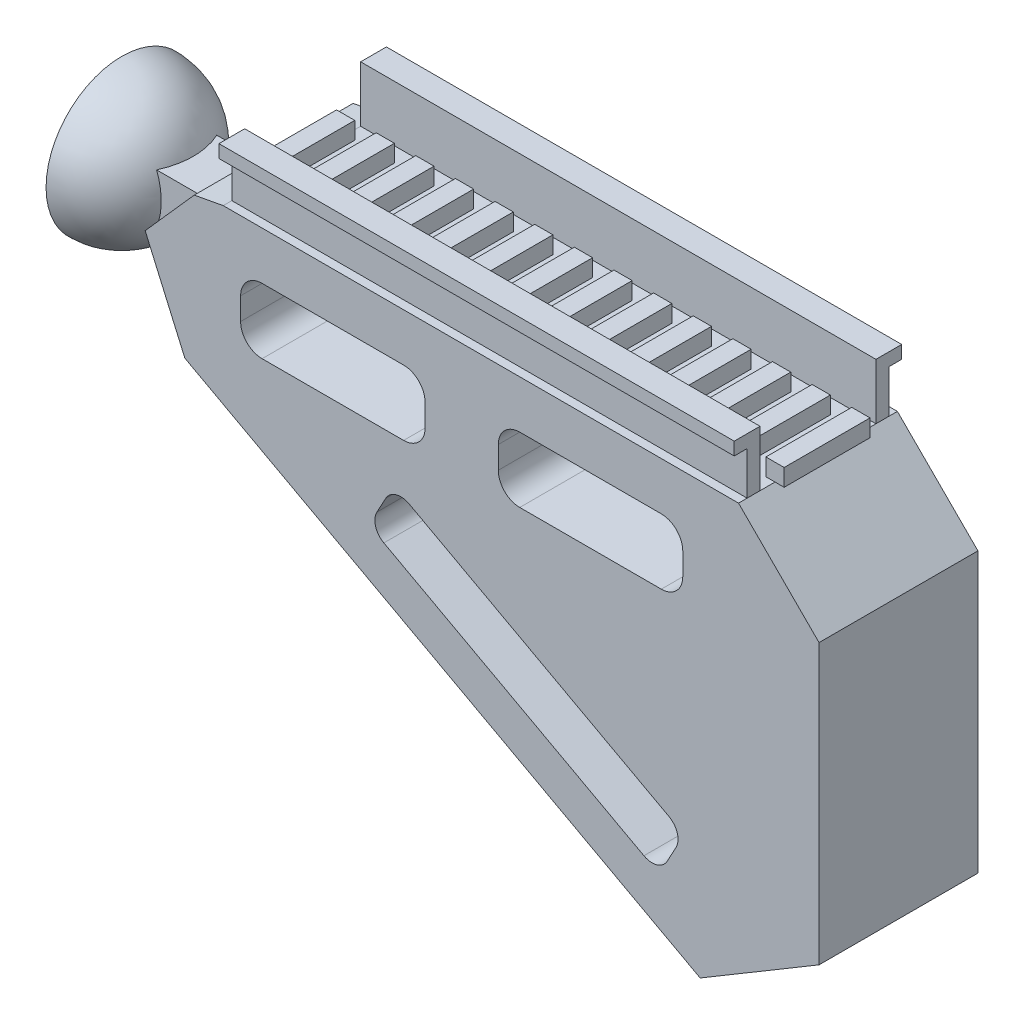
SolidWorks part; units mm, degrees
ref_plane "Front Plane" through (0, 0, 0) normal (0, 0, 1) x (1, 0, 0)
ref_plane "Top Plane" through (0, 0, 0) normal (0, 1, 0) x (1, 0, 0)
ref_plane "Right Plane" through (0, 0, 0) normal (1, 0, 0) x (0, 0, -1)
sketch "Sketch2" plane through (0, 0, 0) normal (1, 0, 0) x (0, 0, -1)
  line L1 (0, 599.7384) -> (0, 1107.4807) construction
sketch "Sketch3" plane through (0, 0, 0) normal (0, 0, 1) x (1, 0, 0)
  line L0 (-305, 571.402) -> (305, 571.402) construction
  point P3 (0, 571.402)
sketch "Sketch8" plane through (0, 0, 0) normal (0, 0, 1) x (1, 0, 0)
  line L0 (0, 18.7499) -> (-119.9998, 18.7499)
  line L5 (-119.9998, 18.7499) -> (-126.7514, 17.4921)
  line L8 (-128.9301, -16.4869) -> (-8.9302, -81.4866)
  line L11 (18.7499, 0) -> (18.7499, -65)
  line L12 (-138.1752, 4.6062) -> (-128.9301, -16.4869)
  line L14 (-8.9302, -81.4866) -> (18.7499, -65)
  line L17 (0, 18.7499) -> (18.7499, 0)
  line L18 (-126.7514, 17.4921) -> (-138.1752, 4.6062)
  dimension "D1" = 119.9998
  dimension "D4" = 18.7499
  dimension "D6" = 16.4866
  dimension "D7" = 27.6801
  dimension "D9" = 65
  dimension "D12" = 9.2451
  dimension "D13" = 12.8859
  dimension "D5" = 18.7499
  dimension "D2" = 65
  dimension "D3" = 119.9998
  dimension "D8" = 18.7499
  dimension "D10" = 64.9998
  dimension "D11" = 21.093
  dimension "D14" = 11.4238
  dimension "D15" = 6.7516
extrude "Boss-Extrude1" add sketch "Sketch8" along normal blind 37
sketch "Sketch10" plane through (0, 0, 0) normal (0, 0, 1) x (1, 0, 0)
  line L0 (-50.9451, -7.596) -> (-17.9852, -7.596)
  line L3 (-110.9451, 7.596) -> (-77.9852, 7.596)
  line L6 (-12.9852, 2.596) -> (-12.9852, -2.596)
  line L11 (-115.9451, 2.596) -> (-115.9451, -2.596)
  line L12 (-110.9451, -7.596) -> (-77.9852, -7.596)
  line L13 (-72.9852, 2.596) -> (-72.9852, -2.596)
  line L14 (-50.9451, 7.596) -> (-17.9852, 7.596)
  line L15 (-55.9451, 2.596) -> (-55.9451, -2.596)
  arc A8 (-110.9451, 7.596) -> (-115.9451, 2.596) centre (-110.9451, 2.596) ccw
  arc A9 (-77.9852, 7.596) -> (-72.9852, 2.596) centre (-77.9852, 2.596) cw
  arc A10 (-77.9852, -7.596) -> (-72.9852, -2.596) centre (-77.9852, -2.596) ccw
  arc A11 (-115.9451, -2.596) -> (-110.9451, -7.596) centre (-110.9451, -2.596) ccw
  arc A12 (-17.9852, -7.596) -> (-12.9852, -2.596) centre (-17.9852, -2.596) ccw
  arc A13 (-17.9852, 7.596) -> (-12.9852, 2.596) centre (-17.9852, 2.596) cw
  arc A14 (-50.9451, 7.596) -> (-55.9451, 2.596) centre (-50.9451, 2.596) ccw
  arc A15 (-55.9451, -2.596) -> (-50.9451, -7.596) centre (-50.9451, -2.596) ccw
  dimension "D3" = 5
  dimension "D4" = 5
  dimension "D5" = 5.1921
  dimension "D6" = 32.9598
  dimension "D2" = 7.596
  dimension "D8" = 27.0402
  dimension "D1" = 77.9852
  dimension "D7" = 2
extrude "Cut-Extrude1" cut sketch "Sketch10" against normal blind 1 and the other way up to surface (37 mm away) other way up to face at (-60.6609, -12.9219, 37)
ref_plane "Plane1" through (0, 18.7499, 0) normal (0, 1, 0) x (1, 0, 0)
sketch "Sketch13" plane through (0, 18.7499, 0) normal (0, 1, 0) x (1, 0, 0)
  line L1 (-2.125, -8.5) -> (2.125, -8.5)
  line L2 (-2.125, -8.5) -> (-2.125, -28.5)
  line L3 (-2.125, -28.5) -> (2.125, -28.5)
  line L4 (2.125, -8.5) -> (2.125, -28.5)
  line L5 (-2.125, -8.5) -> (2.125, -28.5) construction
  line L6 (-2.125, -28.5) -> (2.125, -8.5) construction
  line L7 (-11.355, -8.5) -> (-7.105, -8.5)
  line L8 (-11.355, -8.5) -> (-11.355, -28.5)
  line L9 (-11.355, -28.5) -> (-7.105, -28.5)
  line L10 (-7.105, -8.5) -> (-7.105, -28.5)
  line L11 (-11.355, -8.5) -> (-7.105, -28.5) construction
  line L12 (-11.355, -28.5) -> (-7.105, -8.5) construction
  line L13 (-20.585, -8.5) -> (-16.335, -8.5)
  line L14 (-20.585, -8.5) -> (-20.585, -28.5)
  line L15 (-20.585, -28.5) -> (-16.335, -28.5)
  line L16 (-16.335, -8.5) -> (-16.335, -28.5)
  line L17 (-20.585, -8.5) -> (-16.335, -28.5) construction
  line L18 (-20.585, -28.5) -> (-16.335, -8.5) construction
  line L19 (-29.815, -8.5) -> (-25.565, -8.5)
  line L20 (-29.815, -8.5) -> (-29.815, -28.5)
  line L21 (-29.815, -28.5) -> (-25.565, -28.5)
  line L22 (-25.565, -8.5) -> (-25.565, -28.5)
  line L23 (-29.815, -8.5) -> (-25.565, -28.5) construction
  line L24 (-29.815, -28.5) -> (-25.565, -8.5) construction
  line L25 (-39.045, -8.5) -> (-34.795, -8.5)
  line L26 (-39.045, -8.5) -> (-39.045, -28.5)
  line L27 (-39.045, -28.5) -> (-34.795, -28.5)
  line L28 (-34.795, -8.5) -> (-34.795, -28.5)
  line L29 (-39.045, -8.5) -> (-34.795, -28.5) construction
  line L30 (-39.045, -28.5) -> (-34.795, -8.5) construction
  line L31 (-48.275, -8.5) -> (-44.025, -8.5)
  line L32 (-48.275, -8.5) -> (-48.275, -28.5)
  line L33 (-48.275, -28.5) -> (-44.025, -28.5)
  line L34 (-44.025, -8.5) -> (-44.025, -28.5)
  line L35 (-48.275, -8.5) -> (-44.025, -28.5) construction
  line L36 (-48.275, -28.5) -> (-44.025, -8.5) construction
  line L37 (-57.505, -8.5) -> (-53.255, -8.5)
  line L38 (-57.505, -8.5) -> (-57.505, -28.5)
  line L39 (-57.505, -28.5) -> (-53.255, -28.5)
  line L40 (-53.255, -8.5) -> (-53.255, -28.5)
  line L41 (-57.505, -8.5) -> (-53.255, -28.5) construction
  line L42 (-57.505, -28.5) -> (-53.255, -8.5) construction
  line L43 (-66.735, -8.5) -> (-62.485, -8.5)
  line L44 (-66.735, -8.5) -> (-66.735, -28.5)
  line L45 (-66.735, -28.5) -> (-62.485, -28.5)
  line L46 (-62.485, -8.5) -> (-62.485, -28.5)
  line L47 (-66.735, -8.5) -> (-62.485, -28.5) construction
  line L48 (-66.735, -28.5) -> (-62.485, -8.5) construction
  line L49 (-75.965, -8.5) -> (-71.715, -8.5)
  line L50 (-75.965, -8.5) -> (-75.965, -28.5)
  line L51 (-75.965, -28.5) -> (-71.715, -28.5)
  line L52 (-71.715, -8.5) -> (-71.715, -28.5)
  line L53 (-75.965, -8.5) -> (-71.715, -28.5) construction
  line L54 (-75.965, -28.5) -> (-71.715, -8.5) construction
  line L55 (-85.195, -8.5) -> (-80.945, -8.5)
  line L56 (-85.195, -8.5) -> (-85.195, -28.5)
  line L57 (-85.195, -28.5) -> (-80.945, -28.5)
  line L58 (-80.945, -8.5) -> (-80.945, -28.5)
  line L59 (-85.195, -8.5) -> (-80.945, -28.5) construction
  line L60 (-85.195, -28.5) -> (-80.945, -8.5) construction
  line L61 (-94.425, -8.5) -> (-90.175, -8.5)
  line L62 (-94.425, -8.5) -> (-94.425, -28.5)
  line L63 (-94.425, -28.5) -> (-90.175, -28.5)
  line L64 (-90.175, -8.5) -> (-90.175, -28.5)
  line L65 (-94.425, -8.5) -> (-90.175, -28.5) construction
  line L66 (-94.425, -28.5) -> (-90.175, -8.5) construction
  line L67 (-103.655, -8.5) -> (-99.405, -8.5)
  line L68 (-103.655, -8.5) -> (-103.655, -28.5)
  line L69 (-103.655, -28.5) -> (-99.405, -28.5)
  line L70 (-99.405, -8.5) -> (-99.405, -28.5)
  line L71 (-103.655, -8.5) -> (-99.405, -28.5) construction
  line L72 (-103.655, -28.5) -> (-99.405, -8.5) construction
  line L73 (-112.885, -8.5) -> (-108.635, -8.5)
  line L74 (-112.885, -8.5) -> (-112.885, -28.5)
  line L75 (-112.885, -28.5) -> (-108.635, -28.5)
  line L76 (-108.635, -8.5) -> (-108.635, -28.5)
  line L77 (-112.885, -8.5) -> (-108.635, -28.5) construction
  line L78 (-112.885, -28.5) -> (-108.635, -8.5) construction
  line L79 (-122.115, -8.5) -> (-117.865, -8.5)
  line L80 (-122.115, -8.5) -> (-122.115, -28.5)
  line L81 (-122.115, -28.5) -> (-117.865, -28.5)
  line L82 (-117.865, -8.5) -> (-117.865, -28.5)
  line L83 (-122.115, -8.5) -> (-117.865, -28.5) construction
  line L84 (-122.115, -28.5) -> (-117.865, -8.5) construction
  point P0 (0, -18.5)
  point P9 (-9.23, -18.5)
  point P14 (-18.46, -18.5)
  point P19 (-27.69, -18.5)
  point P24 (-36.92, -18.5)
  point P29 (-46.15, -18.5)
  point P34 (-55.38, -18.5)
  point P39 (-64.61, -18.5)
  point P44 (-73.84, -18.5)
  point P49 (-83.07, -18.5)
  point P54 (-92.3, -18.5)
  point P59 (-101.53, -18.5)
  point P64 (-110.76, -18.5)
  point P69 (-119.99, -18.5)
  dimension "D1" = 4.25
  dimension "D2" = 20
  dimension "D4" = 2.125
  dimension "D5" = 8.5
  dimension "D6" = 4.98
  dimension "D3" = 14
extrude "Boss-Extrude3" add sketch "Sketch13" along normal blind 4 from surface at 0 starting at face at (-59.9999, 18.7499, 18.5)
ref_plane "Plane2" through (-132.115, 0, 0) normal (-1, 0, 0) x (0, 0, 1)
ref_plane "Plane3" through (-162.115, 0, 0) normal (-1, 0, 0) x (0, 0, 1)
sketch "Sketch23" plane through (-162.115, 0, 0) normal (-1, 0, 0) x (0, 0, 1)
  line L0 (18.5023, 18.5528) -> (18.5023, 15.1814)
  line L1 (18.5023, -13.3454) -> (18.5023, -16.7168)
  line L2 (18.5023, 19.7198) -> (18.5023, -18.316) construction
  arc A2 (18.5023, 15.1814) -> (18.5023, -13.3454) centre (18.5023, 0.918) ccw
  arc A3 (18.5023, -16.7168) -> (18.5023, 18.5528) centre (18.5023, 0.918) cw
  point P2 (0.8675, 0.918)
  dimension "D1" = 18.5528
  dimension "D2" = 18.5023
  dimension "D4" = 14.2634
  dimension "D5" = 17.6348
  dimension "D3" = 3.3714
  dimension "D6" = 3.3714
  dimension "D7" = 18.5023
  dimension "D8" = 28.5269
  dimension "D9" = 17.6348
revolve "Revolve4" add sketch "Sketch23" angle 180 about L2
sketch "Sketch24" plane through (-132.115, 0, 0) normal (-1, 0, 0) x (0, 0, 1)
  line L0 (18.5023, 200019.7198) -> (18.5023, -200018.316) construction
  line L1 (11.5023, 6.7019) -> (25.5023, 6.7019)
  line L2 (11.5023, 6.7019) -> (11.5023, -5.2981)
  line L3 (11.5023, -5.2981) -> (25.5023, -5.2981)
  line L4 (25.5023, 6.7019) -> (25.5023, -5.2981)
  line L5 (11.5023, 6.7019) -> (25.5023, -5.2981) construction
  line L6 (11.5023, -5.2981) -> (25.5023, 6.7019) construction
  point P0 (18.5023, 0.7019)
  dimension "D1" = 12
  dimension "D2" = 14
extrude "Boss-Extrude5" add sketch "Sketch24" along normal up to surface (14.8827 mm away)
sketch "Sketch25" plane through (0, 0, 0) normal (1, 0, 0) x (0, 0, -1)
  line L0 (-32, 31.7499) -> (-32, 18.7499)
  line L1 (-18.5, 18.6291) -> (-18.5, 40.0374) construction
  line L2 (-35, 18.7499) -> (-35, 28.7499)
  line L4 (-35, 28.7499) -> (-38, 28.7499)
  line L5 (-38, 28.7499) -> (-38, 31.7499)
  line L6 (-38, 31.7499) -> (-32, 31.7499)
  line L8 (1, 31.7499) -> (-5, 31.7499)
  line L9 (1, 28.7499) -> (1, 31.7499)
  line L10 (-2, 28.7499) -> (1, 28.7499)
  line L11 (-2, 18.7499) -> (-2, 28.7499)
  line L12 (-5, 31.7499) -> (-5, 18.7499)
  line L13 (-35, 18.7499) -> (-32, 18.7499)
  line L14 (-5, 18.7499) -> (-2, 18.7499)
  dimension "D1" = 13
  dimension "D2" = 6
  dimension "D3" = 3
  dimension "D4" = 3
  dimension "D5" = 32
  dimension "D6" = 18.7499
  dimension "D7" = 13.5
extrude "Boss-Extrude6" add sketch "Sketch25" against normal blind 120
sketch "Sketch26" plane through (0, 0, 0) normal (0, 0, 1) x (1, 0, 0)
  line L1 (-128.9301, -16.4869) -> (-8.9302, -81.4866) construction
  line L2 (-68.9302, -48.9867) -> (-54.2673, -21.9168) construction
  line L3 (-82.1572, -21.3719) -> (-84.2052, -25.1528)
  line L4 (-82.5931, -30.5751) -> (-22.0305, -63.3798)
  line L5 (-16.6082, -61.7678) -> (-14.5602, -57.9868)
  line L6 (-16.1723, -52.5645) -> (-76.7349, -19.7598)
  arc A0 (-22.0305, -63.3798) -> (-16.6082, -61.7678) centre (-20.1254, -59.8626) ccw
  arc A1 (-14.5602, -57.9868) -> (-16.1723, -52.5645) centre (-18.0774, -56.0817) ccw
  arc A2 (-84.2052, -25.1528) -> (-82.5931, -30.5751) centre (-80.688, -27.058) ccw
  arc A3 (-76.7349, -19.7598) -> (-82.1572, -21.3719) centre (-78.64, -23.277) ccw
  dimension "D1" = 4
  dimension "D2" = 60.5626
  dimension "D3" = 32.8047
  dimension "D6" = 3.781
  dimension "D8" = 52.5645
  dimension "D9" = 16.1723
extrude "Cut-Extrude2" cut sketch "Sketch26" along normal up to surface (37 mm away) from surface at 0 up to face at (-60.6609, -12.9219, 37) starting at face at (-34.4652, 0, 0)
ref_plane "Plane4" through (0, 0, 18.5) normal (0, 0, 1) x (1, 0, 0)
sketch "Sketch27" plane through (0, 0, 18.5) normal (0, 0, 1) x (1, 0, 0)
  line L0 (-83.1812, -23.2623) -> (-15.5842, -59.8773)
  line L1 (-84.2052, -25.1528) -> (-82.1572, -21.3719) construction
  line L2 (-14.5602, -57.9868) -> (-16.6082, -61.7678) construction
revolve "Revolve-Thin1" add sketch "Sketch27" angle 360 about L0 wall 4
